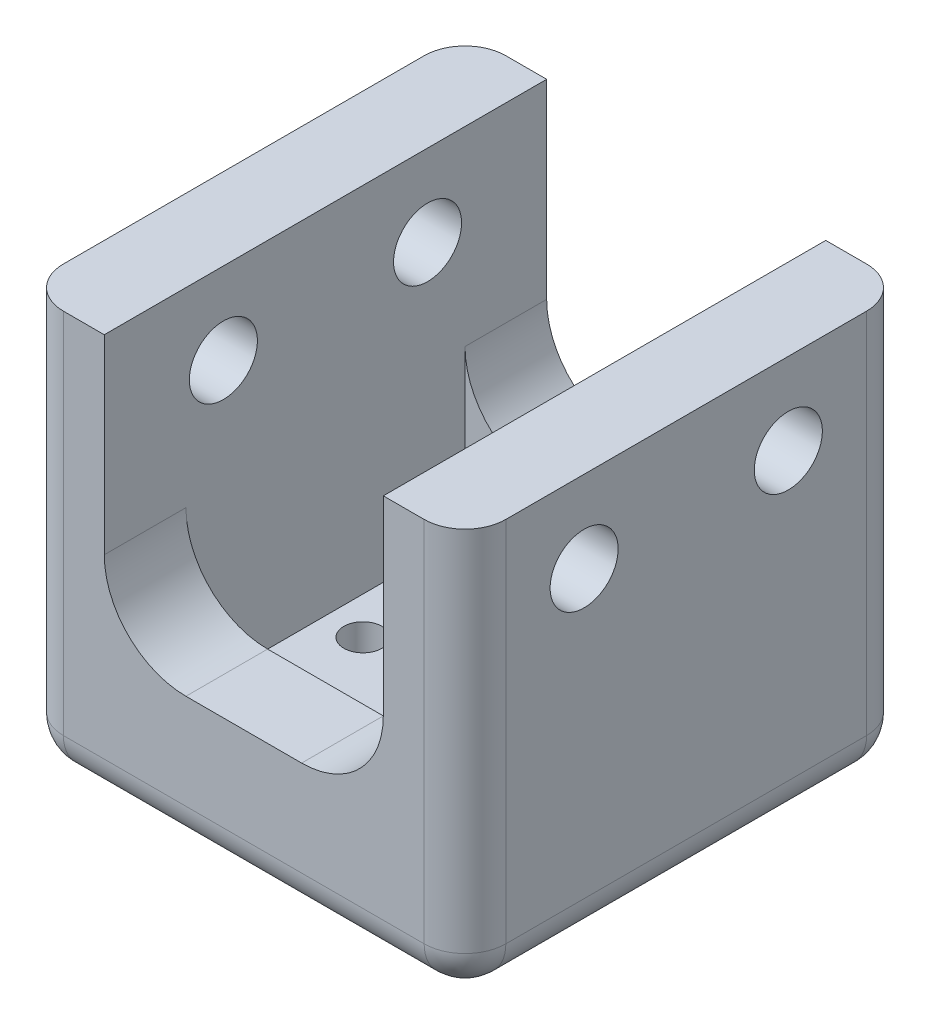
SolidWorks part; units mm, degrees
ref_plane "Front Plane" through (0, 0, 0) normal (0, 0, 1) x (1, 0, 0)
ref_plane "Top Plane" through (0, 0, 0) normal (0, 1, 0) x (1, 0, 0)
ref_plane "Right Plane" through (0, 0, 0) normal (1, 0, 0) x (0, 0, -1)
sketch "Sketch1" plane through (0, 0, 0) normal (0, 1, 0) x (1, 0, 0)
  line L0 (0, 9.525) -> (0, -9.525) construction
  line L5 (9.525, 0) -> (-9.525, 0) construction
  line L9 (-13.0175, -13.0175) -> (13.0175, -13.0175)
  line L10 (-13.0175, -13.0175) -> (-13.0175, 13.0175)
  line L11 (-13.0175, 13.0175) -> (13.0175, 13.0175)
  line L12 (13.0175, -13.0175) -> (13.0175, 13.0175)
  circle A0 centre (0, 9.525) radius 1.778
  circle A1 centre (-9.525, 0) radius 1.778
  circle A2 centre (9.525, 0) radius 1.778
  circle A3 centre (0, -9.525) radius 1.778
  point P4 (-13.0175, 0)
  point P6 (0, -13.0175)
  point P11 (0, 0)
  point P12 (0, 0)
  dimension "D5" = 3.556
  dimension "D1" = 26.035
  dimension "D2" = 26.035
  dimension "D3" = 19.05
  dimension "D4" = 19.05
extrude "Boss-Extrude1" add sketch "Sketch1" along normal blind 5.08
sketch "Sketch9" plane through (0, 0, 0) normal (0, -1, 0) x (1, 0, 0)
  line L22 (20.6375, -20.6375) -> (20.6375, 20.6375)
  line L23 (-13.0175, -13.0175) -> (13.0175, -13.0175)
  line L24 (-13.0175, -13.0175) -> (-13.0175, 13.0175)
  line L25 (-13.0175, 13.0175) -> (13.0175, 13.0175)
  line L26 (13.0175, -13.0175) -> (13.0175, 13.0175)
  line L27 (-20.6375, 20.6375) -> (20.6375, 20.6375)
  line L28 (-20.6375, -20.6375) -> (-20.6375, 20.6375)
  line L29 (-20.6375, -20.6375) -> (20.6375, -20.6375)
  dimension "D1" = 7.62
extrude "Boss-Extrude7" add sketch "Sketch9" against normal blind 38.1
sketch "Sketch10" plane through (0, 0, 20.6375) normal (0, 0, 1) x (1, 0, 0)
  line L0 (-13.0175, 20.32) -> (-13.0175, 38.1)
  line L1 (20.6375, 38.1) -> (-20.6375, 38.1) construction
  line L2 (-13.0175, 38.1) -> (13.0175, 38.1)
  line L3 (13.0175, 38.1) -> (13.0175, 20.32)
  line L4 (5.3975, 12.7) -> (-5.3975, 12.7)
  arc A0 (13.0175, 20.32) -> (5.3975, 12.7) centre (5.3975, 20.32) cw
  arc A1 (-13.0175, 20.32) -> (-5.3975, 12.7) centre (-5.3975, 20.32) ccw
  point P10 (0, 38.1)
  point P11 (0, 38.1)
  dimension "D1" = 7.62
  dimension "D2" = 26.035
  dimension "D3" = 25.4
extrude "Cut-Extrude4" cut sketch "Sketch10" against normal through all
sketch "Sketch11" plane through (-20.6375, 0, 0) normal (-1, 0, 0) x (0, 0, 1)
  line L0 (-9.525, 30.48) -> (9.525, 30.48) construction
  line L1 (20.6375, 38.1) -> (-20.6375, 38.1) construction
  circle A0 centre (-9.525, 30.48) radius 3.175
  circle A1 centre (9.525, 30.48) radius 3.175
  point P4 (0, 30.48)
  point P7 (0, 38.1)
  dimension "D1" = 6.35
  dimension "D2" = 19.05
  dimension "D3" = 17.78
extrude "Cut-Extrude5" cut sketch "Sketch11" against normal through all
fillet "Fillet1" radius 3.81 4 edges at (20.6375, 19.05, -20.6375) (20.6375, 19.05, 20.6375) (-20.6375, 19.05, -20.6375) (-20.6375, 19.05, 20.6375)
fillet "Fillet2" radius 3.81 8 edges at (19.5216, 0, 19.5216) (20.6375, 0, 0) (19.5216, 0, -19.5216) (0, 0, -20.6375) (-19.5216, 0, -19.5216) (-20.6375, 0, 0) (-19.5216, 0, 19.5216) (0, 0, 20.6375)
